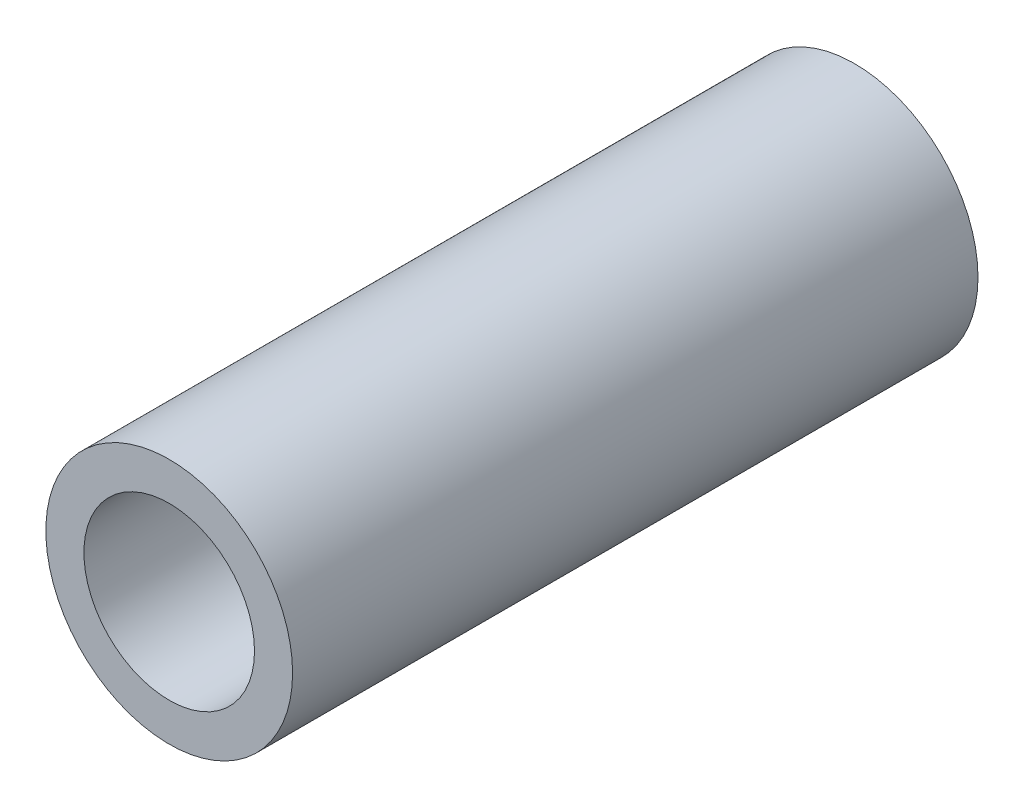
SolidWorks part; units mm, degrees
ref_plane "前视基准面" through (0, 0, 0) normal (0, 0, 1) x (1, 0, 0)
ref_plane "上视基准面" through (0, 0, 0) normal (0, 1, 0) x (1, 0, 0)
ref_plane "右视基准面" through (0, 0, 0) normal (1, 0, 0) x (0, 0, -1)
other "Configuration Table"
sketch "草图1" plane through (0, 0, 0) normal (0, 0, 1) x (1, 0, 0)
  line L0 (0, 0) -> (74.0427, 0)
  line L2 (13.9062, 20.9223) -> (31.4489, 20.9223)
  line L3 (13.9062, 20.9223) -> (13.9062, 9.5711)
  line L4 (13.9062, 9.5711) -> (31.4489, 9.5711)
  line L5 (31.4489, 20.9223) -> (31.4489, 9.5711)
  line L6 (13.9062, 20.9223) -> (31.4489, 9.5711) construction
  line L7 (13.9062, 9.5711) -> (31.4489, 20.9223) construction
  line L8 (48.9917, -6.4237) -> (76.8537, -6.4237)
  line L9 (48.9917, -6.4237) -> (48.9917, -18.7037)
  line L10 (48.9917, -18.7037) -> (76.8537, -18.7037)
  line L11 (76.8537, -6.4237) -> (76.8537, -18.7037)
  line L12 (28.7659, -10.2419) -> (36.5054, -10.2419)
  line L13 (28.7659, -10.2419) -> (28.7659, -11.8929)
  line L14 (28.7659, -11.8929) -> (36.5054, -11.8929)
  line L15 (36.5054, -10.2419) -> (36.5054, -11.8929)
  circle A0 centre (-11.2188, 18.0595) radius 6.4799
  point P3 (22.6776, 15.2467)
  dimension "D1" = 11.3512
extrude "凸台-拉伸1" add sketch "草图1" along normal blind 36 contours A0
sketch "草图2" plane through (0, 0, 36) normal (0, 0, 1) x (1, 0, 0)
  circle A6 centre (-11.2188, 18.0595) radius 4.4799
  circle A7 centre (-11.2188, 18.0595) radius 4.4799
  dimension "D1" = 2
extrude "切除-拉伸1" cut sketch "草图2" against normal up to next
